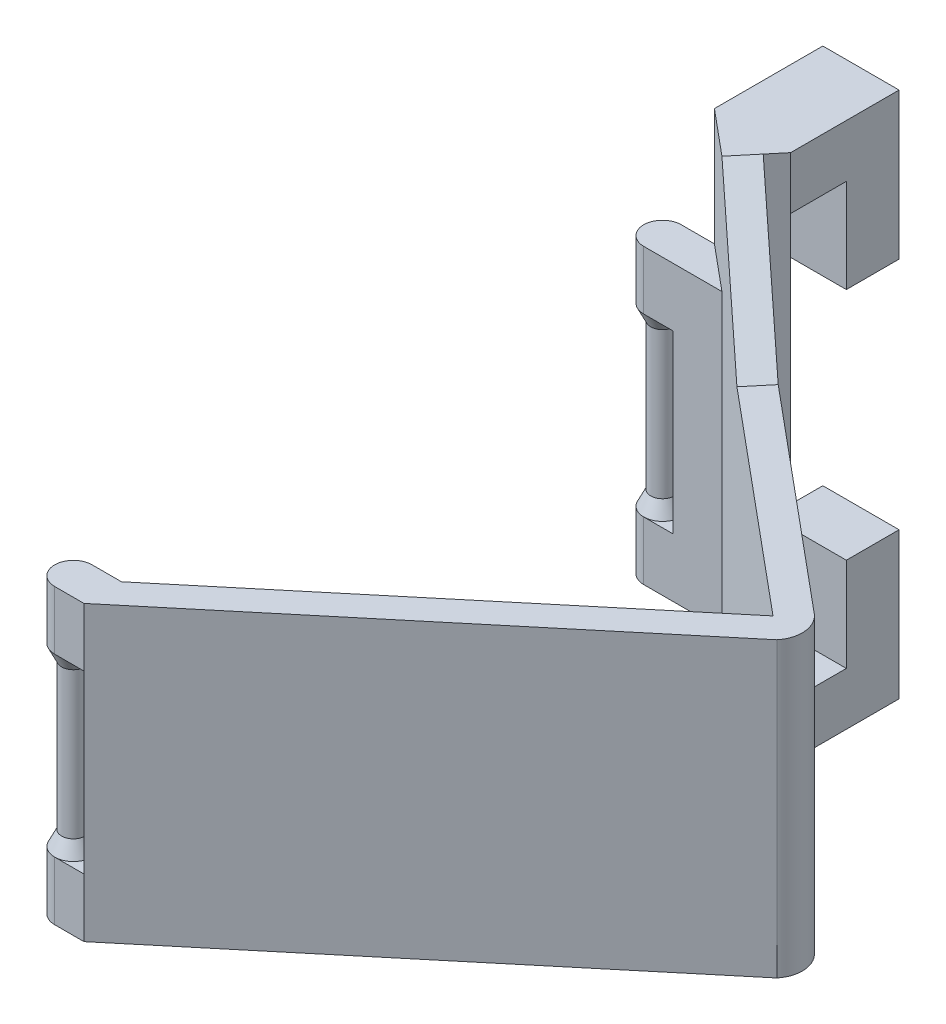
SolidWorks part; units mm, degrees
ref_plane "前视基准面" through (0, 0, 0) normal (0, 0, 1) x (1, 0, 0)
ref_plane "上视基准面" through (0, 0, 0) normal (0, 1, 0) x (1, 0, 0)
ref_plane "右视基准面" through (0, 0, 0) normal (1, 0, 0) x (0, 0, -1)
sketch "草图1" plane through (0, 0, 0) normal (0, 1, 0) x (1, 0, 0)
  line L0 (0, 0) -> (0, 50)
  line L1 (0, 0) -> (-0.664, -50.5533)
  line L2 (0, 0) -> (60, 0)
  line L3 (60, 0) -> (-0.664, -50.5533)
  line L4 (0, 50) -> (60, 0)
  line L5 (60, 0) -> (63.2009, 3.8411)
  line L6 (63.2009, 3.8411) -> (7.8102, 50)
  line L7 (60, 0) -> (63.8411, -3.2009)
  line L8 (63.8411, -3.2009) -> (7.6822, -50)
  line L9 (0, 50) -> (7.8102, 50)
  line L11 (7.6822, -50) -> (-0.664, -56.9551)
  line L12 (-0.664, -56.9551) -> (-0.664, -50.5533)
  arc A0 (63.2009, 3.8411) -> (63.8411, -3.2009) centre (60, 0) cw
extrude "凸台-拉伸1" add sketch "草图1" along normal blind 50
sketch "草图3" plane through (27.7911, 0, -33.3493) normal (0.6402, 0, -0.7682) x (-0.7682, 0, -0.6402)
  line L0 (-46.0933, 25) -> (26.0092, 25) construction
  line L1 (-46.0933, 50) -> (-46.0933, 0) construction
  line L2 (26.0092, 50) -> (26.0092, 0) construction
ref_plane "基准面1" through (0, 25, 0) normal (0, -1, 0) x (-0.7682, 0, -0.6402)
sketch "草图4" plane through (0, 50, 0) normal (0, 1, 0) x (1, 0, 0)
  line L0 (0, 50) -> (7.6822, 43.5982)
  line L1 (0, 50) -> (60, 0) construction
  line L2 (7.6822, 43.5982) -> (10.8831, 47.4393)
  line L3 (63.2009, 3.8411) -> (7.8102, 50) construction
  line L4 (10.8831, 47.4393) -> (7.8102, 50)
  line L5 (7.8102, 50) -> (0, 50)
  line L6 (7.8102, 50) -> (19.6167, 50)
  line L7 (10.8831, 47.4393) -> (13.0171, 50)
  line M4 (63.2009, 3.8411) -> (7.8102, 50)
  line M5 (7.8102, 50) -> (0, 50)
  line M6 (0, 50) -> (60, 0)
extrude "凸台-拉伸3" add sketch "草图4" along normal blind 20 and the other way blind 50 contours L2 M6 M4 M5 | L7 L6 M4
sketch "草图5" plane through (0, 0, -50) normal (0, 0, -1) x (-1, 0, 0)
  line L0 (-13.0171, 70) -> (-13.0171, 61)
  line L1 (-13.0171, 0) -> (-13.0171, 70) construction
  line L2 (-13.0171, 61) -> (0, 61)
  line L3 (0, 70) -> (0, 0) construction
  line L4 (0, 61) -> (0, 70)
  line L5 (0, 70) -> (-13.0171, 70)
extrude "凸台-拉伸4" add sketch "草图5" along normal blind 18.5
sketch "草图6" plane through (0, 61, 0) normal (0, -1, 0) x (1, 0, 0)
  line L0 (0, -68.5) -> (0, -59.5)
  line L1 (0, -68.5) -> (0, -50) construction
  line L2 (13.0171, -68.5) -> (0, -68.5) construction
  line L3 (0, -59.5) -> (13.0171, -59.5)
  line L4 (13.0171, -68.5) -> (13.0171, -50) construction
  line L5 (13.0171, -59.5) -> (13.0171, -68.5)
  line L6 (13.0171, -68.5) -> (0, -68.5)
extrude "凸台-拉伸5" add sketch "草图6" along normal blind 16
mirror "镜向4" about plane through (0, 25, 0) normal (0, -1, 0) of "凸台-拉伸5", "凸台-拉伸3", "凸台-拉伸4"
sketch "草图7" plane through (0, 50, 0) normal (0, 1, 0) x (1, 0, 0)
  line L0 (-0.664, -53.7542) -> (-5.664, -53.7542)
  line L1 (-0.664, -56.9551) -> (-0.664, -50.5533) construction
  line L2 (-5.664, -53.7542) -> (-5.664, 89.3377)
sketch "草图8" plane through (0, 50, 0) normal (0, 1, 0) x (1, 0, 0)
  line L0 (-0.664, -50.5533) -> (-0.664, 65.3859)
  line L1 (7.6822, 43.5982) -> (-0.664, 43.5982)
  line L2 (-0.664, 43.5982) -> (-0.664, 50)
  line L3 (-0.664, 50) -> (0, 50)
  line L4 (0, 50) -> (7.6822, 43.5982)
extrude "凸台-拉伸6" add sketch "草图8" against normal blind 50 contours L1 L2 L3 L4
sketch "草图9" plane through (0, 0, 0) normal (0, -1, 0) x (1, 0, 0)
  line L0 (-0.664, 56.9551) -> (-5.664, 56.9551)
  line L1 (-0.664, 50.5533) -> (-5.664, 50.5533)
  line L2 (-5.664, 53.7542) -> (-5.664, -89.3377) construction
  line L3 (-0.664, 56.9551) -> (-0.664, 50.5533)
  line L4 (-5.664, 56.9551) -> (-5.664, 50.5533)
  arc A0 (-5.664, 56.9551) -> (-5.664, 50.5533) centre (-5.664, 53.7542) ccw
  line M5 (-0.664, 56.9551) -> (-0.664, 50.5533)
extrude "凸台-拉伸7" add sketch "草图9" against normal blind 10 contours L0 L4 L1 M5 | L4 A0
sketch "草图10" plane through (0, 0, 0) normal (0, -1, 0) x (1, 0, 0)
  line L0 (-0.664, -43.5982) -> (-5.664, -43.5982)
  line L1 (-5.664, 53.7542) -> (-5.664, -89.3377) construction
  line L2 (-0.664, -50) -> (-5.664, -50)
  line L3 (-5.664, -43.5982) -> (-5.664, -50)
  arc A0 (-5.664, -43.5982) -> (-5.664, -50) centre (-5.664, -46.7991) ccw
  line M3 (-0.664, -43.5982) -> (-0.664, -50)
extrude "凸台-拉伸8" add sketch "草图10" against normal blind 10 contours L0 L3 L2 M3 | L3 A0
mirror "镜向5" about plane through (0, 25, 0) normal (0, -1, 0) of "凸台-拉伸8", "凸台-拉伸7"
sketch "草图11" plane through (0, 40, 0) normal (0, -1, 0) x (1, 0, 0)
  circle A0 centre (-5.664, 53.7542) radius 2
extrude "凸台-拉伸9" add sketch "草图11" along normal blind 30
ref_plane "基准面3" through (0, 0, 53.7542) normal (0, 0, -1) x (-1, 0, 0)
sketch "草图14" plane through (0, 0, 53.7542) normal (0, 0, -1) x (-1, 0, 0)
  line L5 (7.664, 10) -> (8.8649, 10)
  line L6 (7.664, 10) -> (7.664, 12.5)
  line L7 (7.664, 10) -> (7.664, 40) construction
  line L8 (7.664, 12.5) -> (8.8649, 10)
ref_axis "基准轴2" through (-5.664, 10, 53.7542) along (0, 1, 0)
revolve "旋转1" add sketch "草图14" angle 360 about axis through (-5.664, 10, 53.7542) along (0, 1, 0)
mirror "镜向6" about plane through (0, 25, 0) normal (0, -1, 0) of "旋转1"
sketch "草图15" plane through (0, 10, 0) normal (0, 1, 0) x (1, 0, 0)
  circle A0 centre (-5.664, 46.7991) radius 2
extrude "凸台-拉伸10" add sketch "草图15" along normal blind 30
sketch "草图16" plane through (0, 0, 0) normal (0, -1, 0) x (1, 0, 0)
  line L0 (-5.664, -46.7991) -> (2.4555, -46.7991)
ref_plane "基准面4" through (0, 0, -46.7991) normal (0, 0, 1) x (1, 0, 0)
ref_axis "基准轴3" through (-5.664, 40, -46.7991) along (0, -1, 0)
sketch "草图17" plane through (0, 0, -46.7991) normal (0, 0, 1) x (1, 0, 0)
  line L0 (-7.664, 10) -> (-7.664, 12.5)
  line L1 (-5.664, 10) -> (-8.8649, 10) construction
  line L2 (-7.664, 12.5) -> (-8.8649, 10)
  line L3 (-8.8649, 10) -> (-7.664, 10)
revolve "旋转2" add sketch "草图17" angle 360 about axis through (-5.664, 40, -46.7991) along (0, -1, 0)
mirror "镜向7" about plane through (0, 25, 0) normal (0, -1, 0) of "旋转2"
sketch "草图18" plane through (24.5902, 0, -29.5082) normal (-0.6402, 0, 0.7682) x (0.7682, 0, 0.6402)
  line L0 (-22.0092, 50) -> (-22.0092, 70)
  line L1 (-22.0092, 50) -> (-2.0092, 50)
  line L2 (-22.0092, 50) -> (46.0933, 50) construction
  line L3 (-2.0092, 50) -> (-22.0092, 70)
extrude "凸台-拉伸11" add sketch "草图18" against normal blind 5
mirror "镜向8" about plane through (0, 25, 0) normal (0, -1, 0) of "凸台-拉伸11"
